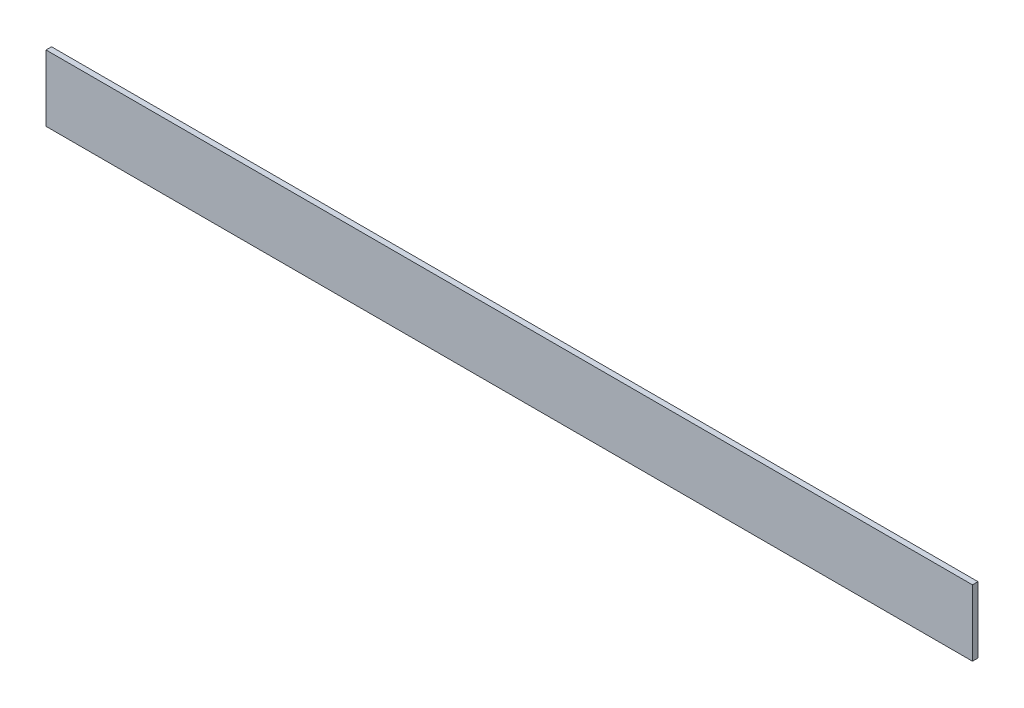
SolidWorks part; units mm, degrees
material "PVC 0.007 Plasticized"
ref_plane "Front Plane" through (0, 0, 0) normal (0, 0, 1) x (1, 0, 0)
ref_plane "Top Plane" through (0, 0, 0) normal (0, 1, 0) x (1, 0, 0)
ref_plane "Right Plane" through (0, 0, 0) normal (1, 0, 0) x (0, 0, -1)
sketch "Sketch1" plane through (0, 0, 0) normal (1, 0, 0) x (0, 0, -1)
  line L1 (-3.175, -38.1) -> (3.175, -38.1)
  line L2 (-3.175, -38.1) -> (-3.175, 38.1)
  line L3 (-3.175, 38.1) -> (3.175, 38.1)
  line L4 (3.175, -38.1) -> (3.175, 38.1)
  line L5 (-3.175, -38.1) -> (3.175, 38.1) construction
  line L6 (-3.175, 38.1) -> (3.175, -38.1) construction
  point P0 (0, 0)
  dimension "D1" = 76.2
  dimension "D2" = 6.35
extrude "Boss-Extrude1" add sketch "Sketch1" along normal blind 1066.8
equation "\"D2@Sketch1\"=1in/4"
